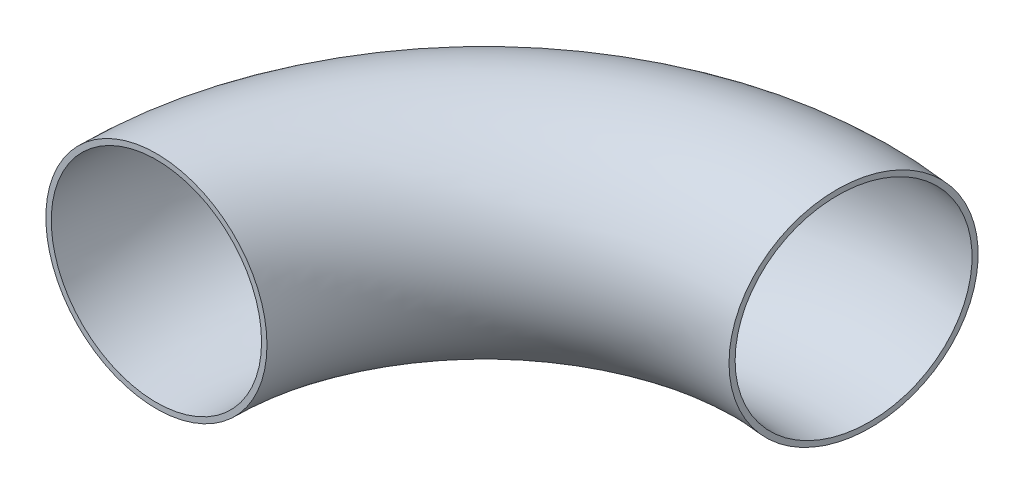
SolidWorks part; units mm, degrees
material "Plain Carbon Steel"
ref_plane "Front Plane" through (0, 0, 0) normal (0, 0, 1) x (1, 0, 0)
ref_plane "Top Plane" through (0, 0, 0) normal (0, 1, 0) x (1, 0, 0)
ref_plane "Right Plane" through (0, 0, 0) normal (1, 0, 0) x (0, 0, -1)
sketch "Sketch1" plane through (0, 0, 0) normal (0, 0, 1) x (1, 0, 0)
  circle A0 centre (0, 0) radius 25.4
  circle A1 centre (0, 0) radius 24.1554
  dimension "D1" = 1.2446
sketch "Sketch3" plane through (0, 0, 0) normal (0, 1, 0) x (1, 0, 0)
  arc A0 (0, 0) -> (85.5532, 74.6068) centre (75.3071, 0) cw
sweep "Sweep3" add profiles "Sketch1" path "Sketch3"
